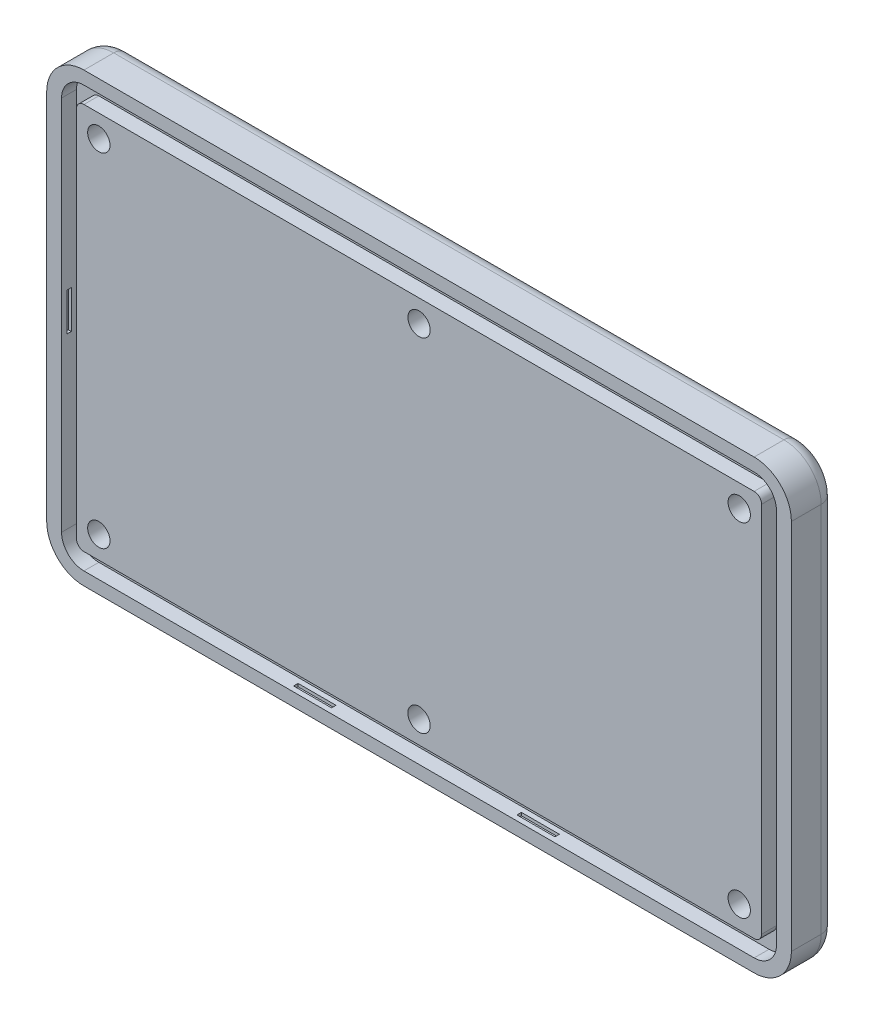
SolidWorks part; units mm, degrees
ref_plane "前视基准面" through (0, 0, 0) normal (0, 0, 1) x (1, 0, 0)
ref_plane "上视基准面" through (0, 0, 0) normal (0, 1, 0) x (1, 0, 0)
ref_plane "右视基准面" through (0, 0, 0) normal (1, 0, 0) x (0, 0, -1)
other "Configuration Table"
sketch "草图1" plane through (0, 0, 0) normal (0, 0, 1) x (1, 0, 0)
  line L1 (50, 30) -> (-50, 30)
  line L2 (50, 30) -> (50, -30)
  line L3 (50, -30) -> (-50, -30)
  line L4 (-50, 30) -> (-50, -30)
  line L5 (50, 30) -> (-50, -30) construction
  line L6 (50, -30) -> (-50, 30) construction
  point P0 (0, 0)
  dimension "D1" = 100
  dimension "D2" = 60
extrude "凸台-拉伸1" add sketch "草图1" along normal blind 6
fillet "圆角1" radius 5 4 edges at (-50, -30, 3) (50, -30, 3) (50, 30, 3) (-50, 30, 3)
fillet "圆角2" radius 2 8 edges at (48.5355, -28.5355, 0) (50, 0, 0) (48.5355, 28.5355, 0) (0, 30, 0) (-48.5355, 28.5355, 0) (-50, 0, 0) (-48.5355, -28.5355, 0) (0, -30, 0)
sketch "草图2" plane through (0, 0, 6) normal (0, 0, 1) x (1, 0, 0)
  line L1 (-45, 28.25) -> (45, 28.25)
  line L2 (-48, 25.25) -> (-48, -25.25)
  line L3 (-45, -28.25) -> (45, -28.25)
  line L4 (48, 25.25) -> (48, -25.25)
  line L5 (-48, 28.25) -> (48, -28.25) construction
  line L6 (-48, -28.25) -> (48, 28.25) construction
  arc A0 (45, -28.25) -> (48, -25.25) centre (45, -25.25) ccw
  arc A1 (48, 25.25) -> (45, 28.25) centre (45, 25.25) ccw
  arc A2 (-45, 28.25) -> (-48, 25.25) centre (-45, 25.25) ccw
  arc A3 (-45, -28.25) -> (-48, -25.25) centre (-45, -25.25) cw
  point P0 (0, 0)
  dimension "D1" = 3
  dimension "D2" = 96
  dimension "D3" = 56.5
extrude "切除-拉伸1" cut sketch "草图2" against normal blind 2
sketch "草图4" plane through (0, -28.25, 0) normal (0, 1, 0) x (1, 0, 0)
  line L0 (45, -5) -> (-45, -5) construction
  line L1 (17.55, -5.3) -> (12.45, -5.3)
  line L2 (17.55, -5.3) -> (17.55, -4.7)
  line L3 (17.55, -4.7) -> (12.45, -4.7)
  line L4 (12.45, -5.3) -> (12.45, -4.7)
  line L5 (17.55, -5.3) -> (12.45, -4.7) construction
  line L6 (17.55, -4.7) -> (12.45, -5.3) construction
  line L10 (-12.45, -5.3) -> (-17.55, -5.3)
  line L11 (-12.45, -5.3) -> (-12.45, -4.7)
  line L12 (-12.45, -4.7) -> (-17.55, -4.7)
  line L13 (-17.55, -5.3) -> (-17.55, -4.7)
  line L14 (-12.45, -5.3) -> (-17.55, -4.7) construction
  line L15 (-12.45, -4.7) -> (-17.55, -5.3) construction
  line L16 (45, -6) -> (45, -2) construction
  line L17 (-45, -2) -> (-45, -6) construction
  line L18 (45, -6) -> (-45, -6) construction
  point P0 (15, -5)
  point P12 (-15, -5)
  dimension "D1" = 1
  dimension "D2" = 0.6
  dimension "D3" = 5.1
  dimension "D4" = 0.6
  dimension "D5" = 5.1
  dimension "D6" = 30
  dimension "D7" = 60
extrude "切除-拉伸2" cut sketch "草图4" against normal blind 0.4
sketch "草图5" plane through (0, 28.25, 0) normal (0, -1, 0) x (1, 0, 0)
  line L0 (-17.55, 5.3) -> (-17.55, 4.7) construction
  line L1 (-12.45, 5.3) -> (-17.55, 5.3) construction
  line L2 (-12.45, 4.7) -> (-17.55, 4.7) construction
  line L3 (-12.45, 5.3) -> (-12.45, 4.7) construction
  line L4 (12.45, 5.3) -> (12.45, 4.7) construction
  line L5 (17.55, 5.3) -> (12.45, 5.3) construction
  line L6 (17.55, 5.3) -> (17.55, 4.7) construction
  line L7 (17.55, 4.7) -> (12.45, 4.7) construction
  line L8 (-17.55, 5.3) -> (-17.55, 4.7)
  line L9 (-12.45, 5.3) -> (-17.55, 5.3)
  line L10 (-12.45, 4.7) -> (-17.55, 4.7)
  line L11 (-12.45, 5.3) -> (-12.45, 4.7)
  line L12 (12.45, 5.3) -> (12.45, 4.7)
  line L13 (17.55, 5.3) -> (12.45, 5.3)
  line L14 (17.55, 5.3) -> (17.55, 4.7)
  line L15 (17.55, 4.7) -> (12.45, 4.7)
extrude "切除-拉伸3" cut sketch "草图5" against normal blind 0.4
sketch "草图6" plane through (-48, 0, 0) normal (1, 0, 0) x (0, 0, -1)
  line L0 (-6, -25) -> (-2, -25) construction
  line L1 (-5, -25) -> (-5, 25) construction
  line L2 (-2, 25) -> (-6, 25) construction
  line L3 (-6, -25) -> (-6, 25) construction
  line L5 (-5.3, -2.55) -> (-4.7, -2.55)
  line L6 (-5.3, -2.55) -> (-5.3, 2.55)
  line L7 (-5.3, 2.55) -> (-4.7, 2.55)
  line L8 (-4.7, -2.55) -> (-4.7, 2.55)
  line L9 (-5.3, -2.55) -> (-4.7, 2.55) construction
  line L10 (-5.3, 2.55) -> (-4.7, -2.55) construction
  point P8 (-5, 0)
  point P15 (-5, 0)
  dimension "D1" = 1
  dimension "D2" = 5.1
  dimension "D3" = 0.6
extrude "切除-拉伸4" cut sketch "草图6" against normal blind 0.4
sketch "草图7" plane through (48, 0, 0) normal (-1, 0, 0) x (0, 0, 1)
  line L0 (5.3, 2.55) -> (4.7, 2.55) construction
  line L1 (5.3, -2.55) -> (4.7, -2.55) construction
  line L2 (5.3, -2.55) -> (5.3, 2.55) construction
  line L3 (4.7, -2.55) -> (4.7, 2.55) construction
  line L4 (5.3, 2.55) -> (4.7, 2.55)
  line L5 (5.3, -2.55) -> (4.7, -2.55)
  line L6 (5.3, -2.55) -> (5.3, 2.55)
  line L7 (4.7, -2.55) -> (4.7, 2.55)
extrude "切除-拉伸5" cut sketch "草图7" against normal blind 0.4
sketch "草图8" plane through (0, 0, 4) normal (0, 0, 1) x (1, 0, 0)
  line L1 (45, -26) -> (-45, -26)
  line L2 (46, -25) -> (46, 25)
  line L3 (45, 26) -> (-45, 26)
  line L4 (-46, -25) -> (-46, 25)
  line L5 (46, -26) -> (-46, 26) construction
  line L6 (46, 26) -> (-46, -26) construction
  arc A0 (-46, 25) -> (-45, 26) centre (-45, 25) cw
  arc A1 (-46, -25) -> (-45, -26) centre (-45, -25) ccw
  arc A2 (46, -25) -> (45, -26) centre (45, -25) cw
  arc A3 (45, 26) -> (46, 25) centre (45, 25) cw
  point P0 (0, 0)
  dimension "D3" = 1
  dimension "D1" = 92
  dimension "D2" = 52
extrude "凸台-拉伸2" add sketch "草图8" along normal blind 2
sketch "草图9" plane through (0, 0, 6) normal (0, 0, 1) x (1, 0, 0)
  line L0 (46, -25) -> (46, 25) construction
  line L1 (45, 26) -> (-45, 26) construction
  line L2 (0, 2.2273) -> (0, 28.2273) construction
  line L4 (0, 0) -> (46, 0) construction
  circle A0 centre (43, 23) radius 1.5
  circle A1 centre (0, 23) radius 1.5
  circle A2 centre (-43, 23) radius 1.5
  circle A3 centre (-43, -23) radius 1.5
  circle A4 centre (0, -23) radius 1.5
  circle A5 centre (43, -23) radius 1.5
  dimension "D1" = 3
  dimension "D4" = 3
  dimension "D2" = 3
  dimension "D3" = 3
  dimension "D5" = 3
extrude "切除-拉伸6" cut sketch "草图9" against normal up to next
sketch "草图10" plane through (0, 0, 0) normal (0, 0, -1) x (-1, 0, 0)
  circle A0 centre (43, 23) radius 3.05
  circle A1 centre (0, 23) radius 3.05
  circle A2 centre (-43, 23) radius 3.05
  circle A3 centre (-43, -23) radius 3.05
  circle A4 centre (0, -23) radius 3.05
  circle A5 centre (43, -23) radius 3.05
  dimension "D1" = 6.1
extrude "切除-拉伸7" cut sketch "草图10" against normal blind 1.1
fillet "圆角3" radius 0.5 6 edges at (39.95, 23, 0) (39.95, -23, 0) (-3.05, -23, 0) (-3.05, 23, 0) (-46.05, -23, 0) (-46.05, 23, 0)
